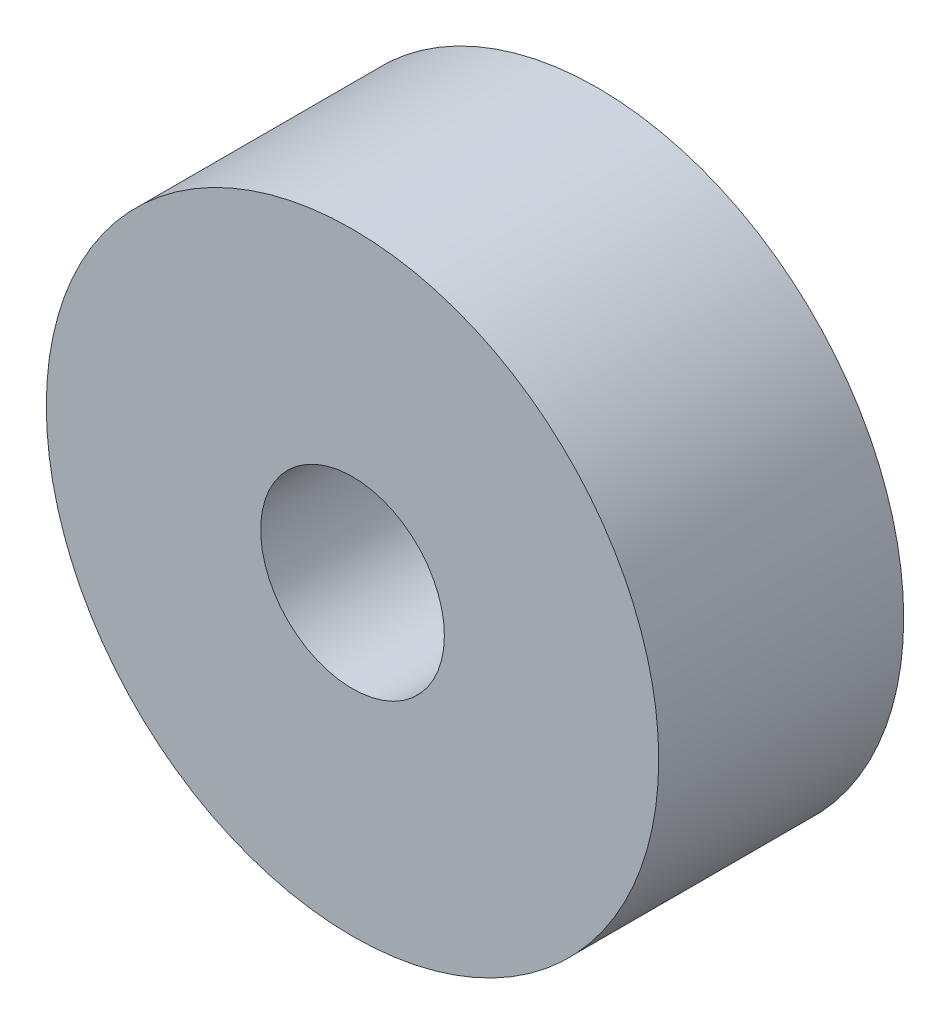
SolidWorks part; units mm, degrees
ref_plane "Спереди" through (0, 0, 0) normal (0, 0, 1) x (1, 0, 0)
ref_plane "Сверху" through (0, 0, 0) normal (0, 1, 0) x (1, 0, 0)
ref_plane "Справа" through (0, 0, 0) normal (1, 0, 0) x (0, 0, -1)
sketch "Эскиз1" plane through (0, 0, 0) normal (0, 0, 1) x (1, 0, 0)
  circle A0 centre (0, 0) radius 5
  circle A1 centre (0, 0) radius 1.5
  dimension "D1" = 10
  dimension "D2" = 3
extrude "Бобышка-Вытянуть1" add sketch "Эскиз1" along normal blind 4
